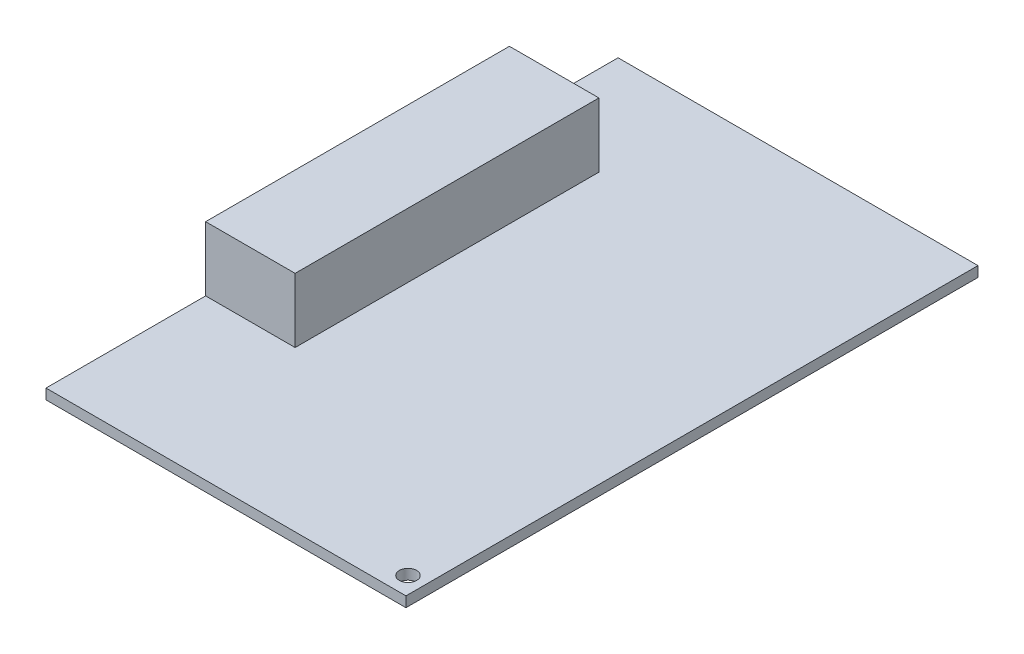
SolidWorks part; units mm, degrees
ref_plane "前视基准面" through (0, 0, 0) normal (0, 0, 1) x (1, 0, 0)
ref_plane "上视基准面" through (0, 0, 0) normal (0, 1, 0) x (1, 0, 0)
ref_plane "右视基准面" through (0, 0, 0) normal (1, 0, 0) x (0, 0, -1)
other "Configuration Table"
sketch "草图1" plane through (0, 0, 0) normal (0, 1, 0) x (1, 0, 0)
  line L1 (-28, -44.5) -> (28, -44.5)
  line L2 (-28, -44.5) -> (-28, 44.5)
  line L3 (-28, 44.5) -> (28, 44.5)
  line L4 (28, -44.5) -> (28, 44.5)
  line L5 (-28, -44.5) -> (28, 44.5) construction
  line L6 (-28, 44.5) -> (28, -44.5) construction
  point P0 (0, 0)
  dimension "D1" = 56
  dimension "D2" = 89
extrude "凸台-拉伸1" add sketch "草图1" along normal blind 1.6
sketch "草图2" plane through (0, 1.6, 0) normal (0, 1, 0) x (1, 0, 0)
  line L0 (-28, 44.5) -> (-28, -44.5) construction
  line L1 (-28, 27.5978) -> (-14.075, 27.5978)
  line L2 (-28, 27.5978) -> (-28, -19.6663)
  line L3 (-28, -19.6663) -> (-14.075, -19.6663)
  line L4 (-14.075, 27.5978) -> (-14.075, -19.6663)
extrude "凸台-拉伸2" add sketch "草图2" along normal blind 10
sketch "草图3" plane through (0, 1.6, 0) normal (0, 1, 0) x (1, 0, 0)
  line L1 (26.76, -44.5) -> (26.76, -35.0596) construction
  line L2 (-28, -44.5) -> (28, -44.5) construction
  line L3 (28, -44.5) -> (28, 44.5) construction
  line L4 (28, -42.94) -> (12.94, -42.94) construction
  circle A0 centre (25.41, -41.59) radius 1.35
  dimension "D1" = 1.24
  dimension "D2" = 2.7
  dimension "D3" = 1.56
extrude "切除-拉伸1" cut sketch "草图3" against normal blind 10
